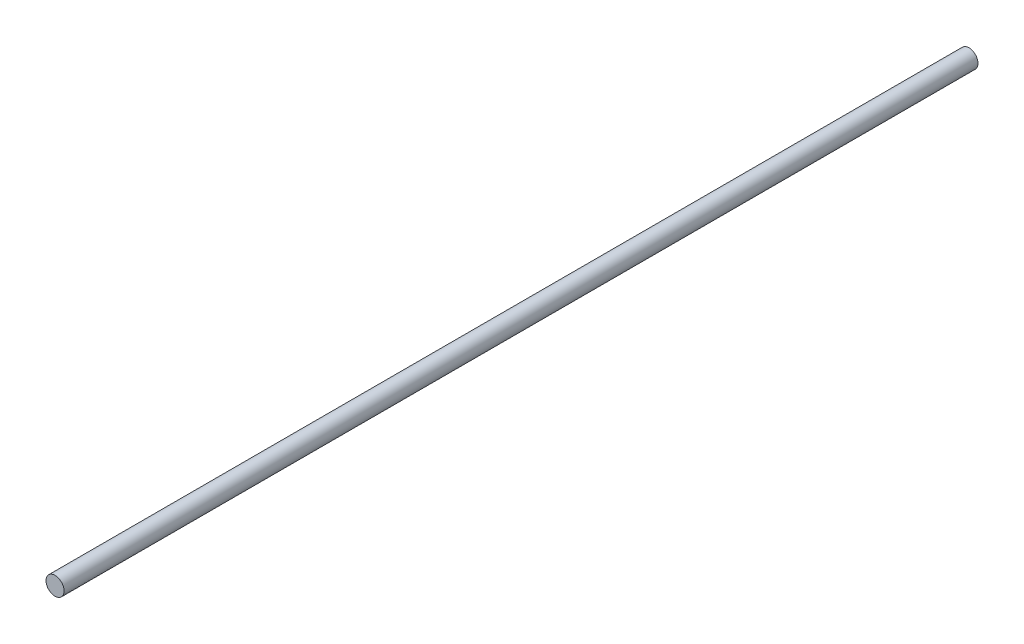
SolidWorks part; units mm, degrees
ref_plane "Alzado" through (0, 0, 0) normal (0, 0, 1) x (1, 0, 0)
ref_plane "Planta" through (0, 0, 0) normal (0, 1, 0) x (1, 0, 0)
ref_plane "Vista lateral" through (0, 0, 0) normal (1, 0, 0) x (0, 0, -1)
sketch "Croquis1" plane through (0, 0, 0) normal (0, 0, 1) x (1, 0, 0)
  circle A0 centre (0, 0) radius 6
  dimension "D1" = 12
extrude "Saliente-Extruir1" add sketch "Croquis1" along normal blind 605.8
